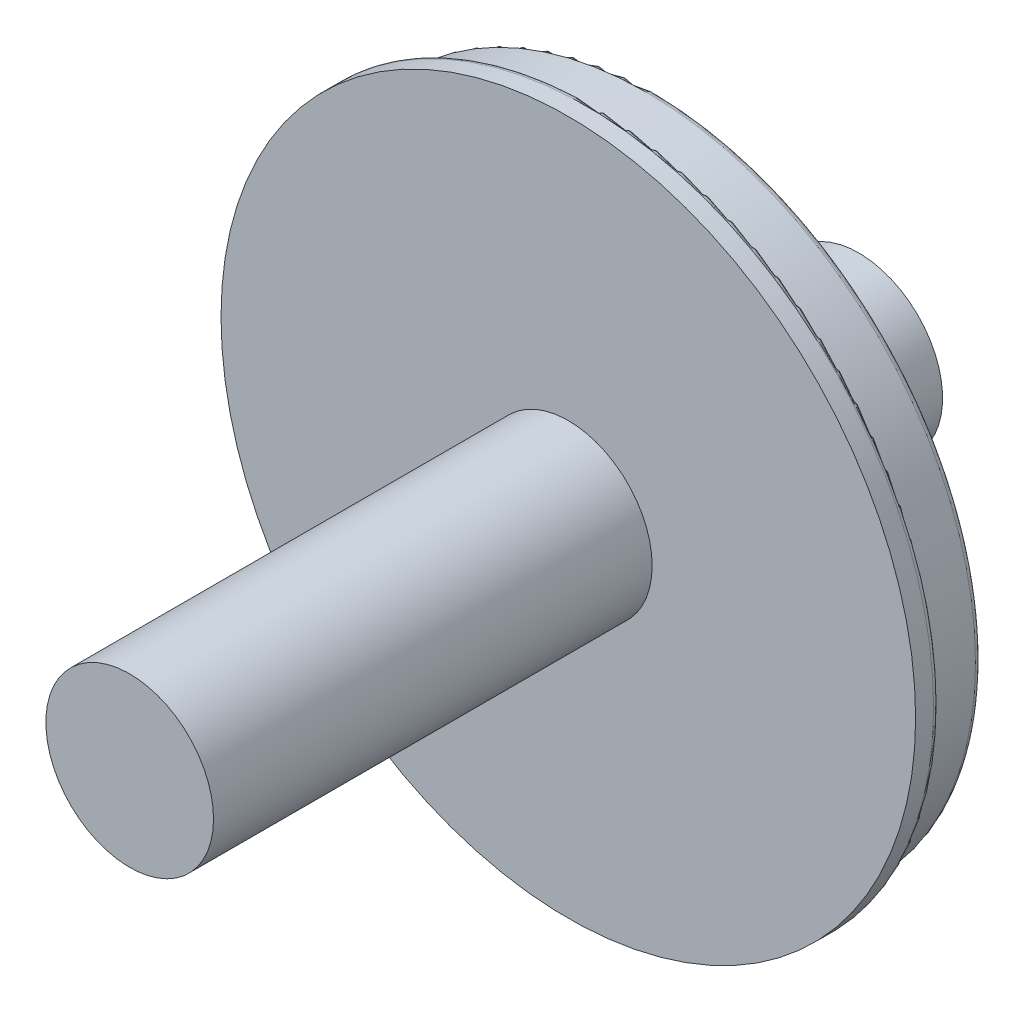
SolidWorks part; units mm, degrees
ref_plane "Piano frontale" through (0, 0, 0) normal (0, 0, 1) x (1, 0, 0)
ref_plane "Piano superiore" through (0, 0, 0) normal (0, 1, 0) x (1, 0, 0)
ref_plane "Piano destro" through (0, 0, 0) normal (1, 0, 0) x (0, 0, -1)
sketch "Schizzo4" plane through (0, 0, 0) normal (0, 0, 1) x (1, 0, 0)
  circle A0 centre (0, 0) radius 580
extrude "Estrusione-Estrusione1" add sketch "Schizzo4" along normal blind 40
sketch "Schizzo5" plane through (0, 0, 0) normal (0, 0, -1) x (-1, 0, 0)
  circle A2 centre (0, 0) radius 550
  circle A3 centre (0, 0) radius 550
  dimension "D1" = 30
extrude "Estrusione-Estrusione2" add sketch "Schizzo5" along normal blind 100
fillet "Raccordo4" radius 10 2 edges at (580, 0, 0) (-550, 0, 0)
fillet "Raccordo3" radius 10 1 edges at (-550, 0, -100)
sketch "Schizzo6" plane through (0, 0, 40) normal (0, 0, 1) x (1, 0, 0)
  circle A0 centre (0, 0) radius 140
extrude "Estrusione-Estrusione3" add sketch "Schizzo6" along normal blind 732.5
sketch "Schizzo8" plane through (0, 0, -100) normal (0, 0, -1) x (-1, 0, 0)
  circle A0 centre (0, 0) radius 140
extrude "Estrusione-Estrusione4" add sketch "Schizzo8" along normal blind 345
sketch3d "Schizzo3D1"
  spline S0 degree 3 poles (-487.4994, -60.6007, -100) (-490.7628, -7.865, -100) (-489.0692, 36.9686, -100) (-484.8918, 73.7288, -100) (-477.9551, 110.068, -100) (-468.2978, 145.7823, -100) (-453.2454, 188.4056, -100) (-430.4436, 236.8277, -100) (-397.3468, 288.937, -100) (-363.211, 330.1604, -100) (-331.0296, 361.9044, -100) (-302.8083, 385.8279, -100) (-272.865, 407.5545, -100) (-241.3674, 426.9627, -100) (-201.2066, 447.7097, -100) (-151.4286, 467.3742, -100) (-91.62, 482.6742, -100) (-30.361, 490.3541, -100) (31.3765, 490.2901, -100) (92.6187, 482.4838, -100) (152.3983, 467.0584, -100) (209.7714, 444.2576, -100) (263.8318, 414.4413, -100) (313.726, 378.0805, -100) (358.666, 335.7492, -100) (397.9423, 288.116, -100) (430.9344, 235.933, -100) (457.1215, 180.0243, -100) (476.0901, 121.2728, -100) (487.5405, 60.6063, -100) (491.292, -1.0174, -100) (487.2853, -62.6249, -100) (475.5837, -123.2435, -100) (456.372, -181.916, -100) (429.9536, -237.7157, -100) (396.7456, -289.7616, -100) (357.2725, -337.2317, -100) (312.1575, -379.3765, -100) (262.1131, -415.5304, -100) (207.9297, -445.1226, -100) (150.4626, -467.6856, -100) (90.6199, -482.8633, -100) (29.345, -490.4156, -100) (-32.3893, -490.2247, -100) (-85.4669, -483.3461, -100) (-129.485, -473.0634, -100) (-164.7758, -461.9577, -100) (-199.1272, -448.2236, -100) (-232.3469, -431.9378, -100) (-271.3209, -409.0392, -100) (-314.5108, -377.4282, -100) (-359.3586, -335.0082, -100) (-393.3219, -293.6426, -100) (-418.352, -256.002, -100) (-436.4594, -223.739, -100) (-452.0822, -190.2043, -100) (-465.1328, -155.5857, -100) (-477.7519, -112.5305, -100) (-487.4994, -60.6007, -100) (-490.7628, -7.865, -100) (-489.0692, 36.9686, -100) knots -0.051376 -0.039364 -0.019682 0 0.012012 0.024024 0.036035 0.048047 0.060059 0.08007 0.100081 0.120092 0.132104 0.144116 0.156127 0.168139 0.180151 0.200162 0.220173 0.240184 0.260195 0.280207 0.300218 0.320229 0.34024 0.360251 0.380262 0.400273 0.420285 0.440296 0.460307 0.480318 0.500329 0.52034 0.540351 0.560363 0.580374 0.600385 0.620396 0.640407 0.660418 0.680429 0.700441 0.720452 0.740463 0.760474 0.780485 0.792497 0.804509 0.81652 0.828532 0.840544 0.860555 0.880566 0.900577 0.912589 0.924601 0.936612 0.948624 0.960636 0.980318 1 1.012012 1.024024 1.036035 only from (-490, 0, -100) to (-490, 0, -100)
  spline S1 degree 3 poles (-487.4994, -60.6007, -100) (-490.7628, -7.865, -100) (-489.0692, 36.9686, -100) (-484.8918, 73.7288, -100) (-477.9551, 110.068, -100) (-468.2978, 145.7823, -100) (-453.2454, 188.4056, -100) (-430.4436, 236.8277, -100) (-397.3468, 288.937, -100) (-363.211, 330.1604, -100) (-331.0296, 361.9044, -100) (-302.8083, 385.8279, -100) (-272.865, 407.5545, -100) (-241.3674, 426.9627, -100) (-201.2066, 447.7097, -100) (-151.4286, 467.3742, -100) (-91.62, 482.6742, -100) (-30.361, 490.3541, -100) (31.3765, 490.2901, -100) (92.6187, 482.4838, -100) (152.3983, 467.0584, -100) (209.7714, 444.2576, -100) (263.8318, 414.4413, -100) (313.726, 378.0805, -100) (358.666, 335.7492, -100) (397.9423, 288.116, -100) (430.9344, 235.933, -100) (457.1215, 180.0243, -100) (476.0901, 121.2728, -100) (487.5405, 60.6063, -100) (491.292, -1.0174, -100) (487.2853, -62.6249, -100) (475.5837, -123.2435, -100) (456.372, -181.916, -100) (429.9536, -237.7157, -100) (396.7456, -289.7616, -100) (357.2725, -337.2317, -100) (312.1575, -379.3765, -100) (262.1131, -415.5304, -100) (207.9297, -445.1226, -100) (150.4626, -467.6856, -100) (90.6199, -482.8633, -100) (29.345, -490.4156, -100) (-32.3893, -490.2247, -100) (-85.4669, -483.3461, -100) (-129.485, -473.0634, -100) (-164.7758, -461.9577, -100) (-199.1272, -448.2236, -100) (-232.3469, -431.9378, -100) (-271.3209, -409.0392, -100) (-314.5108, -377.4282, -100) (-359.3586, -335.0082, -100) (-393.3219, -293.6426, -100) (-418.352, -256.002, -100) (-436.4594, -223.739, -100) (-452.0822, -190.2043, -100) (-465.1328, -155.5857, -100) (-477.7519, -112.5305, -100) (-487.4994, -60.6007, -100) (-490.7628, -7.865, -100) (-489.0692, 36.9686, -100) knots -0.051376 -0.039364 -0.019682 0 0.012012 0.024024 0.036035 0.048047 0.060059 0.08007 0.100081 0.120092 0.132104 0.144116 0.156127 0.168139 0.180151 0.200162 0.220173 0.240184 0.260195 0.280207 0.300218 0.320229 0.34024 0.360251 0.380262 0.400273 0.420285 0.440296 0.460307 0.480318 0.500329 0.52034 0.540351 0.560363 0.580374 0.600385 0.620396 0.640407 0.660418 0.680429 0.700441 0.720452 0.740463 0.760474 0.780485 0.792497 0.804509 0.81652 0.828532 0.840544 0.860555 0.880566 0.900577 0.912589 0.924601 0.936612 0.948624 0.960636 0.980318 1 1.012012 1.024024 1.036035 only from (-490, 0, -100) to (-490, 0, -100)
  dimension "D1" = 50
extrude "Taglio-Estrusione2" cut sketch "Schizzo3D1" along direction (0, 0, -1) on the side of the normal blind 20
